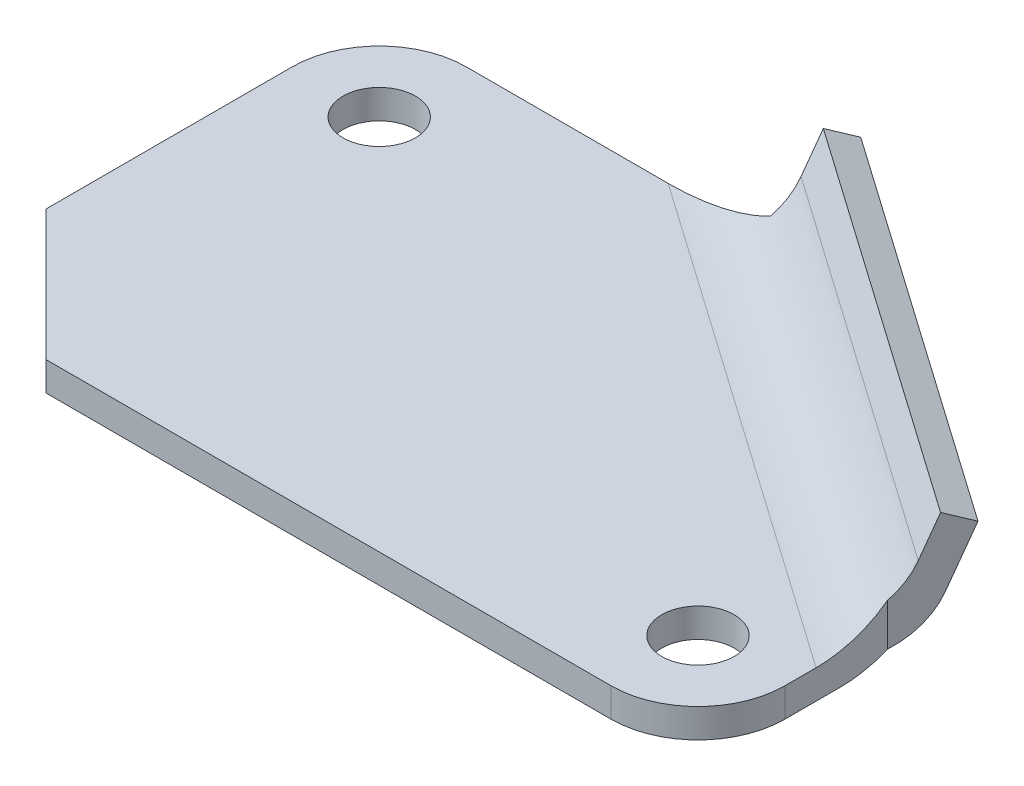
SolidWorks part; units mm, degrees
ref_plane "Front Plane" through (0, 0, 0) normal (0, 0, 1) x (1, 0, 0)
ref_plane "Top Plane" through (0, 0, 0) normal (0, 1, 0) x (1, 0, 0)
ref_plane "Right Plane" through (0, 0, 0) normal (1, 0, 0) x (0, 0, -1)
sketch "Sketch1" plane through (0, 0, 0) normal (0, 1, 0) x (1, 0, 0)
  line L0 (0, 18) -> (18, 0)
  line L1 (18, 0) -> (96, 0)
  line L2 (0, 18) -> (0, 52)
  line L3 (12, 64) -> (54, 64)
  line L4 (108, 12) -> (108, 26.1888)
  line L5 (54, 64) -> (108, 26.1888)
  line L6 (108, 26.1888) -> (126.1133, 52.0573) construction
  arc A0 (96, 0) -> (108, 12) centre (96, 12) ccw
  arc A1 (0, 52) -> (12, 64) centre (12, 52) cw
  circle A2 centre (12, 52) radius 5
  circle A3 centre (96, 12) radius 5
  point P0 (0, 0)
  point P7 (108, 0)
  point P10 (0, 64)
  dimension "D3" = 12
  dimension "D7" = 10
  dimension "D8" = 10
  dimension "D1" = 108
  dimension "D2" = 64
  dimension "D4" = 54
  dimension "D5" = 35
  dimension "D9" = 90
extrude "Boss-Extrude1" add sketch "Sketch1" along normal mid plane 4
sketch "Sketch3" plane through (0, 2, 0) normal (0, 1, 0) x (1, 0, 0)
  line L0 (108, 26.1888) -> (119.6691, 42.854) construction
  line L1 (108, 26.1888) -> (85.8675, 41.6861) construction
  line L2 (108, 26.1888) -> (54, 64) construction
  dimension "D1" = 90
ref_plane "Plane2" through (60.1644, 0, 42.1276) normal (0.8192, 0, 0.5736) x (0.5736, 0, -0.8192)
sketch "Sketch4" plane through (60.1644, 0, 42.1276) normal (0.8192, 0, 0.5736) x (0.5736, 0, -0.8192)
  line L0 (83.3989, 2) -> (88.6434, 14.9806)
  line L1 (88.6434, 14.9806) -> (92.3521, 13.4821)
  line L2 (92.3521, 13.4821) -> (86.0969, -2)
  line L3 (86.0969, -2) -> (83.3989, -2)
  line L4 (81.5622, 2) -> (76.4747, 2) construction
  line L5 (71.7761, 2) -> (83.3989, 2) construction
  line L6 (83.3989, 2) -> (103.7433, 2) construction
  line L7 (83.3989, 2) -> (83.3989, -2)
  dimension "D1" = 4
  dimension "D2" = 14
  dimension "D3" = 112
  dimension "D4" = 68
extrude "Boss-Extrude2" add sketch "Sketch4" against normal up to vertex (65.9218 mm away)
fillet "Fillet1" radius 12 1 edges at (82.5475, -2, -47.3045)
fillet "Fillet2" radius 12 1 edges at (81, 2, -45.0944)
